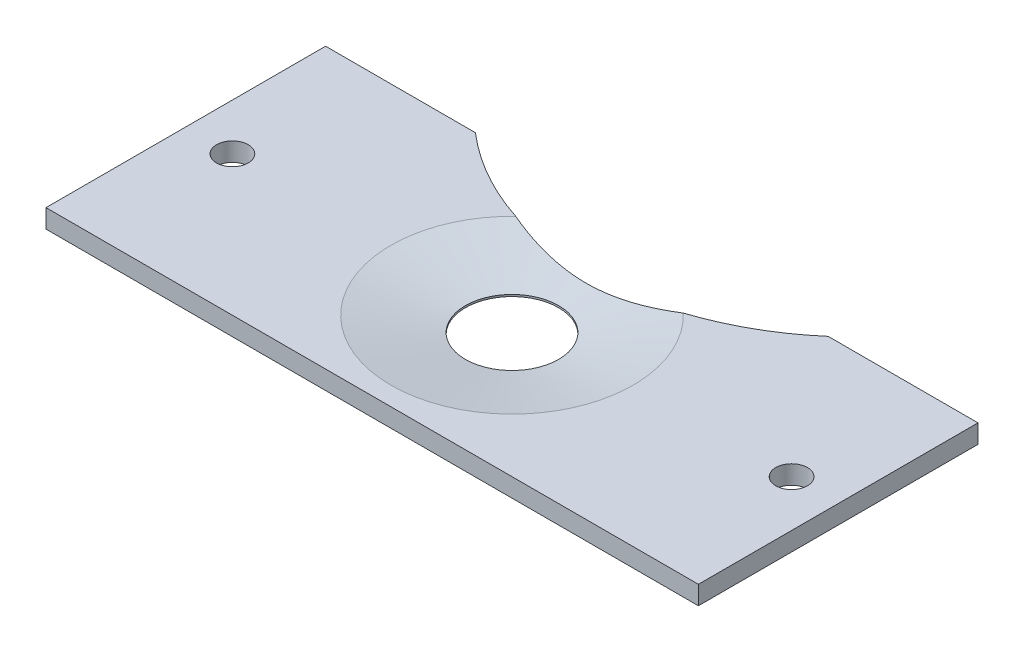
SolidWorks part; units mm, degrees
ref_plane "Front Plane" through (0, 0, 0) normal (0, 0, 1) x (1, 0, 0)
ref_plane "Top Plane" through (0, 0, 0) normal (0, 1, 0) x (1, 0, 0)
ref_plane "Right Plane" through (0, 0, 0) normal (1, 0, 0) x (0, 0, -1)
sketch "Sketch1" plane through (0, 0, 0) normal (0, 1, 0) x (1, 0, 0)
  line L1 (-35, 15) -> (35, 15)
  line L2 (-35, 15) -> (-35, -15)
  line L3 (-35, -15) -> (35, -15)
  line L4 (35, 15) -> (35, -15)
  circle A0 centre (0, 0) radius 5
  dimension "D5" = 10
  dimension "D1" = 35
  dimension "D2" = 35
  dimension "D3" = 15
  dimension "D4" = 15
extrude "Extrude1" add sketch "Sketch1" along normal blind 2
chamfer "Chamfer1" distance 8 distance2 1.6 1 edges at (0, 2, 5)
sketch "Sketch3" plane through (0, 0, 0) normal (0, -1, 0) x (1, 0, 0)
  circle A0 centre (0, 0) radius 5.5
extrude "Cut-Extrude1" cut sketch "Sketch3" against normal blind 0.2
hole_wizard "M3 Clearance Hole1" positions "Sketch6" profile "Sketch5" hole size "M3" standard "ISO" end condition through all
sketch "Sketch6" plane through (0, 2, 0) normal (0, 1, 0) x (-1, 0, 0)
  line L0 (-35, 15) -> (-35, -15) construction
  line L1 (35, -15) -> (35, 15) construction
  line L3 (-35, -15) -> (35, -15) construction
  point P0 (-30, 0)
  point P5 (30, 0)
  dimension "D1" = 5
  dimension "D2" = 5
  dimension "D3" = 15
sketch "Sketch5" plane through (30, 2, 0) normal (1, 0, 0) x (0, 0, 1)
  line L0 (0, 0) -> (0, 2)
  line L1 (0, 2) -> (1.7, 2)
  line L2 (1.7, 2) -> (1.7, 0)
  line L5 (1.7, 0) -> (0, 0)
  line L11 (0, -6.35) -> (0, 107.95) construction
  dimension "Thru Hole Dia." = 3.4
  dimension "Thru Hole Depth" = 2
sketch "Sketch7" plane through (0, 2, 0) normal (0, 1, 0) x (-1, 0, 0)
  circle A0 centre (0, -36.9329) radius 28.9692
extrude "Cut-Extrude2" cut sketch "Sketch7" against normal through all
equation "\"D2@Sketch1\" = \"D1@Sketch1\""
equation "\"D4@Sketch1\" = \"D3@Sketch1\""
equation "\"D2@Sketch6\" = \"D1@Sketch6\""
